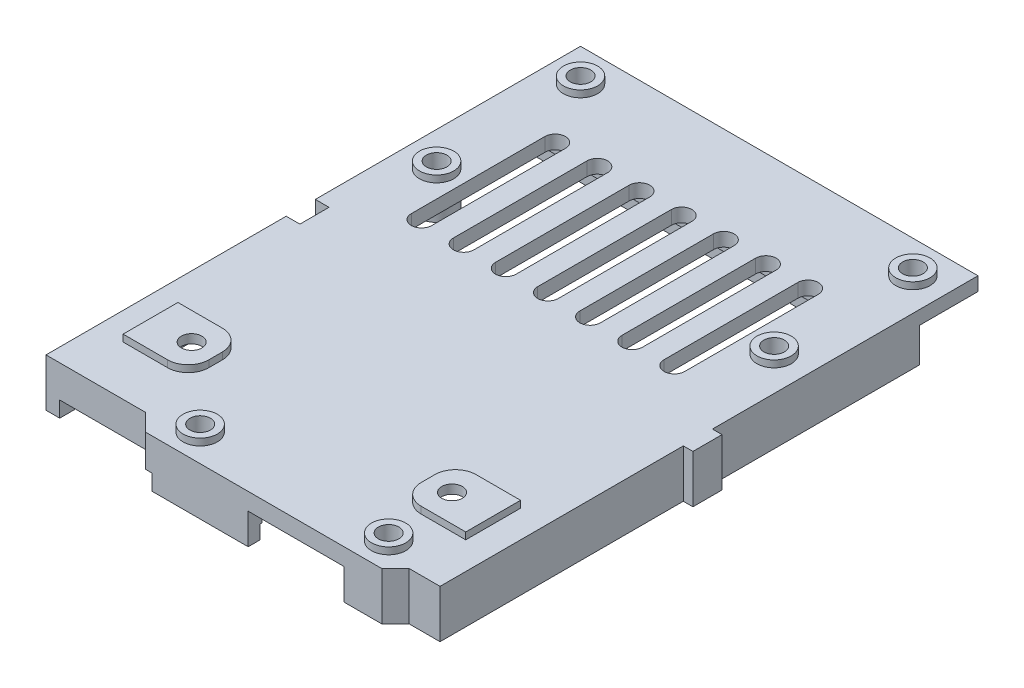
SolidWorks part; units mm, degrees
material "PVC 0.007 Plasticized"
ref_plane "Front Plane" through (0, 0, 0) normal (0, 0, 1) x (1, 0, 0)
ref_plane "Top Plane" through (0, 0, 0) normal (0, 1, 0) x (1, 0, 0)
ref_plane "Right Plane" through (0, 0, 0) normal (1, 0, 0) x (0, 0, -1)
sketch "Sketch1" plane through (0, 0, 0) normal (0, 1, 0) x (1, 0, 0)
  line L0 (0, 40.5) -> (0, 0) construction
  line L1 (-29, 40.5) -> (29, 40.5)
  line L2 (-29, 40.5) -> (-29, -40.5)
  line L3 (-29, -40.5) -> (29, -40.5)
  line L4 (29, 40.5) -> (29, -40.5)
  line L5 (-29, 40.5) -> (29, -40.5) construction
  line L6 (-29, -40.5) -> (29, 40.5) construction
  line L7 (18.2, 26.5) -> (18.2, 7) construction
  line L8 (19.7, 26.5) -> (19.7, 7)
  line L9 (16.7, 26.5) -> (16.7, 7)
  line L10 (12.05, 26.5) -> (12.05, 7) construction
  line L11 (13.55, 26.5) -> (13.55, 7)
  line L12 (10.55, 26.5) -> (10.55, 7)
  line L13 (5.9, 26.5) -> (5.9, 7) construction
  line L14 (7.4, 26.5) -> (7.4, 7)
  line L15 (4.4, 26.5) -> (4.4, 7)
  line L16 (-0.25, 26.5) -> (-0.25, 7) construction
  line L17 (1.25, 26.5) -> (1.25, 7)
  line L18 (-1.75, 26.5) -> (-1.75, 7)
  line L19 (-6.4, 26.5) -> (-6.4, 7) construction
  line L20 (-4.9, 26.5) -> (-4.9, 7)
  line L21 (-7.9, 26.5) -> (-7.9, 7)
  line L22 (-12.55, 26.5) -> (-12.55, 7) construction
  line L23 (-11.05, 26.5) -> (-11.05, 7)
  line L24 (-14.05, 26.5) -> (-14.05, 7)
  line L25 (-18.7, 26.5) -> (-18.7, 7) construction
  line L26 (-17.2, 26.5) -> (-17.2, 7)
  line L27 (-20.2, 26.5) -> (-20.2, 7)
  circle A0 centre (24.25, 35.75) radius 1.5
  circle A1 centre (-24.25, 35.75) radius 1.5
  circle A2 centre (24, 15.75) radius 1.5
  circle A3 centre (-24, 14.5) radius 1.5
  circle A4 centre (19, -26.25) radius 1.5
  circle A5 centre (19.5, -36) radius 1.5
  circle A6 centre (-8, -36) radius 1.5
  circle A7 centre (-19, -26.25) radius 1.5
  arc A8 (19.7, 26.5) -> (16.7, 26.5) centre (18.2, 26.5) ccw
  arc A9 (16.7, 7) -> (19.7, 7) centre (18.2, 7) ccw
  arc A10 (13.55, 26.5) -> (10.55, 26.5) centre (12.05, 26.5) ccw
  arc A11 (10.55, 7) -> (13.55, 7) centre (12.05, 7) ccw
  arc A12 (7.4, 26.5) -> (4.4, 26.5) centre (5.9, 26.5) ccw
  arc A13 (4.4, 7) -> (7.4, 7) centre (5.9, 7) ccw
  arc A14 (1.25, 26.5) -> (-1.75, 26.5) centre (-0.25, 26.5) ccw
  arc A15 (-1.75, 7) -> (1.25, 7) centre (-0.25, 7) ccw
  arc A16 (-4.9, 26.5) -> (-7.9, 26.5) centre (-6.4, 26.5) ccw
  arc A17 (-7.9, 7) -> (-4.9, 7) centre (-6.4, 7) ccw
  arc A18 (-11.05, 26.5) -> (-14.05, 26.5) centre (-12.55, 26.5) ccw
  arc A19 (-14.05, 7) -> (-11.05, 7) centre (-12.55, 7) ccw
  arc A20 (-17.2, 26.5) -> (-20.2, 26.5) centre (-18.7, 26.5) ccw
  arc A21 (-20.2, 7) -> (-17.2, 7) centre (-18.7, 7) ccw
  point P0 (0, 0)
  point P26 (18.2, 16.75)
  point P31 (18.2, 28)
  point P32 (18.2, 5.5)
  point P37 (12.05, 16.75)
  point P44 (5.9, 16.75)
  point P51 (-0.25, 16.75)
  point P58 (-6.4, 16.75)
  point P65 (-12.55, 16.75)
  point P72 (-18.7, 16.75)
  dimension "D3" = 3
  dimension "D6" = 3
  dimension "D9" = 3
  dimension "D12" = 3
  dimension "D17" = 3
  dimension "D26" = 3
  dimension "D1" = 81
  dimension "D2" = 58
  dimension "D4" = 48.5
  dimension "D5" = 62
  dimension "D7" = 5
  dimension "D8" = 20
  dimension "D10" = 38
  dimension "D11" = 14.25
  dimension "D13" = 4.5
  dimension "D14" = 9.5
  dimension "D15" = 27.5
  dimension "D16" = 4.5
  dimension "D18" = 22.5
  dimension "D19" = 3
  dimension "D20" = 12.5
  dimension "D21" = 9.3
  dimension "D23" = 6.15
  dimension "D24" = 5
  dimension "D25" = 21.25
  dimension "D22" = 7
extrude "Boss-Extrude1" add sketch "Sketch1" along normal blind 2
sketch "Sketch2" plane through (0, 0, 0) normal (0, -1, 0) x (1, 0, 0)
  line L0 (-29, -40.5) -> (-29, 40.5) construction
  line L1 (-29, -30) -> (29, -30)
  line L2 (-29, -30) -> (-29, -32)
  line L3 (-29, -32) -> (29, -32)
  line L4 (29, -30) -> (29, -32)
  line L5 (29, 40.5) -> (29, -40.5) construction
  line L6 (29, -40.5) -> (-29, -40.5) construction
  line L7 (24.5, 36) -> (22.5, 38)
  line L8 (29, -30) -> (27, -30)
  line L9 (29, -30) -> (29, 38)
  line L10 (29, 38) -> (27, 38)
  line L11 (27, -30) -> (27, 38)
  line L12 (29, 38) -> (24.5, 38)
  line L13 (29, 38) -> (29, 36)
  line L14 (29, 36) -> (24.5, 36)
  line L15 (24.5, 38) -> (24.5, 36)
  line L16 (22.5, 38) -> (17, 38)
  line L17 (17, 38) -> (17, 40)
  line L18 (17, 40) -> (22.5, 40)
  line L19 (22.5, 40) -> (24.5, 38)
  line L20 (-12, 40) -> (-14.5, 37.5)
  line L21 (17, 40) -> (3, 40)
  line L22 (17, 40) -> (17, 38)
  line L23 (17, 38) -> (3, 38)
  line L24 (3, 40) -> (3, 38)
  line L25 (3, 38) -> (-12, 38)
  line L26 (3, 38) -> (3, 40)
  line L27 (3, 40) -> (-12, 40)
  line L28 (-12, 38) -> (-12, 40)
  line L29 (-12, 37.5) -> (-12, 38)
  line L30 (-29, 37.5) -> (-12, 37.5)
  line L31 (-29, 37.5) -> (-29, 35.5)
  line L32 (-29, 35.5) -> (-12, 35.5)
  line L33 (-12, 37.5) -> (-12, 35.5)
  line L35 (-29, 37.5) -> (-27, 37.5)
  line L36 (-29, 37.5) -> (-29, -32)
  line L37 (-29, -32) -> (-27, -32)
  line L38 (-27, 37.5) -> (-27, -32)
  line M41 (29, -40.5) -> (29, 40.5)
  line M43 (-29, 40.5) -> (-29, -40.5)
  dimension "D1" = 2
  dimension "D2" = 10.5
  dimension "D3" = 68
  dimension "D4" = 2
  dimension "D5" = 4.5
  dimension "D6" = 2
  dimension "D7" = 45
  dimension "D8" = 2
  dimension "D9" = 5.5
  dimension "D10" = 6.5
  dimension "D11" = 2
  dimension "D12" = 14
  dimension "D13" = 15
  dimension "D14" = 45
  dimension "D15" = 2.5
  dimension "D16" = 2
  dimension "D17" = 2
extrude "Boss-Extrude2" add sketch "Sketch2" along normal blind 0.5 contours L21 L24 L23 L17 | L38 L32 L1 M43 | L1 L38 L3 M41 | L38 L1 L3 M43 | L14 L11 L1 M41 | L12 L15 L14 L11 | L14 L9 L10 L11 | L19 L18 L17 L16 L7 L15 | L28 L25 L24 L27 | L20 L30 L29 L28 | L30 L38 L32 L33 | L38 L30 L32 M43
sketch "Sketch5" plane through (0, -0.5, 0) normal (0, -1, 0) x (1, 0, 0)
  line L0 (-27, -30) -> (27, -30)
  line L1 (27, -30) -> (27, 36)
  line L2 (27, 36) -> (24.5, 36)
  line L3 (24.5, 36) -> (22.5, 38)
  line L4 (22.5, 38) -> (17, 38)
  line L5 (17, 38) -> (17, 40)
  line L6 (-11, 38) -> (-11, 40)
  line L7 (-27, 35.5) -> (-27, 37.5)
  line L8 (-27, 35.5) -> (-12, 35.5)
  line L9 (-12, 35.5) -> (-12, 38)
  line L10 (-12, 38) -> (3, 38)
  line L11 (3, 38) -> (3, 40)
  line L12 (-27, 35.5) -> (-27, -30)
  line L16 (22.5, 40) -> (-12, 40)
  line L17 (-12, 40) -> (-14.5, 37.5)
  line L18 (-14.5, 37.5) -> (-29, 37.5)
  line L19 (-29, 37.5) -> (-29, -32)
  line L20 (-29, -32) -> (29, -32)
  line L21 (29, -32) -> (29, 38)
  line L22 (29, 38) -> (24.5, 38)
  line L23 (24.5, 38) -> (22.5, 40)
  line L24 (22.5, 40) -> (-12, 40)
  line L25 (-12, 40) -> (-14.5, 37.5)
  line L26 (-14.5, 37.5) -> (-29, 37.5)
  line L27 (-29, 37.5) -> (-29, -32)
  line L28 (-29, -32) -> (29, -32)
  line L29 (29, -32) -> (29, 38)
  line L30 (29, 38) -> (24.5, 38)
  line L31 (24.5, 38) -> (22.5, 40)
  line M10 (27, -30) -> (-27, -30)
  line M11 (-27, -30) -> (-27, 35.5)
  line M12 (-27, 35.5) -> (-12, 35.5)
  line M13 (-12, 35.5) -> (-12, 38)
  line M14 (-12, 38) -> (22.5, 38)
  line M15 (22.5, 38) -> (24.5, 36)
  line M16 (24.5, 36) -> (27, 36)
  line M17 (27, 36) -> (27, -30)
  line M18 (22.5, 40) -> (-12, 40)
  line M19 (-12, 40) -> (-14.5, 37.5)
  line M20 (-14.5, 37.5) -> (-29, 37.5)
  line M21 (-29, 37.5) -> (-29, -32)
  line M22 (-29, -32) -> (29, -32)
  line M23 (29, -32) -> (29, 38)
  line M24 (29, 38) -> (24.5, 38)
  line M25 (24.5, 38) -> (22.5, 40)
  dimension "D2" = 1
  dimension "D1" = 0
extrude "Boss-Extrude3" add sketch "Sketch5" along normal blind 4.5 contours L6 L5 M14 M18 M19 M20 M21 M22 M23 M24 M25 M15 M16 M17 M10 M11 M12 M13 | L11 L6 M14 M18
sketch "Sketch6" plane through (0, 0, 0) normal (0, -1, 0) x (1, 0, 0)
  line L16 (-11, 38) -> (-11, 40)
  line L17 (-11, 40) -> (-12, 40)
  line L18 (-12, 40) -> (-14.5, 37.5)
  line L19 (-14.5, 37.5) -> (-27, 37.5)
  line L20 (-27, 37.5) -> (-27, 35.5)
  line L21 (-27, 35.5) -> (-12, 35.5)
  line L22 (-12, 35.5) -> (-12, 38)
  line L23 (-12, 38) -> (-11, 38)
  line L24 (-11, 38) -> (-11, 40)
  line L25 (-11, 40) -> (-12, 40)
  line L26 (-12, 40) -> (-14.5, 37.5)
  line L27 (-14.5, 37.5) -> (-27, 37.5)
  line L28 (-27, 37.5) -> (-27, 35.5)
  line L29 (-27, 35.5) -> (-12, 35.5)
  line L30 (-12, 35.5) -> (-12, 38)
  line L31 (-12, 38) -> (-11, 38)
  dimension "D1" = 0
extrude "Boss-Extrude4" add sketch "Sketch6" along normal blind 2.7
sketch "Sketch7" plane through (0, 0, 0) normal (0, -1, 0) x (1, 0, 0)
  line L1 (-25, 30.25) -> (-15.5, 30.25)
  line L2 (-25, 30.25) -> (-25, 22.25)
  line L3 (-25, 22.25) -> (-15.5, 22.25)
  line L4 (-15.5, 30.25) -> (-15.5, 22.25)
  line L5 (-27, -30) -> (-27, 37.5) construction
  line L6 (0, 0) -> (0, 40.5) construction
  line L7 (-29, 40.5) -> (29, 40.5) construction
  line L8 (15.5, 30.25) -> (15.5, 22.25)
  line L9 (25, 22.25) -> (15.5, 22.25)
  line L10 (25, 30.25) -> (25, 22.25)
  line L11 (25, 30.25) -> (15.5, 30.25)
  circle A1 centre (-19, 26.25) radius 1.5
  arc A2 (-18.5, 30.25) -> (-15.5, 27.25) centre (-18.5, 27.25) cw
  arc A3 (-15.5, 25.25) -> (-18.5, 22.25) centre (-18.5, 25.25) cw
  arc A4 (15.5, 25.25) -> (18.5, 22.25) centre (18.5, 25.25) ccw
  arc A5 (18.5, 30.25) -> (15.5, 27.25) centre (18.5, 27.25) ccw
  circle A6 centre (19, 26.25) radius 1.5
  point P10 (-15.5, 26.25)
  circle M32 centre (19, 26.25) radius 1.5
  circle M35 centre (-19, 26.25) radius 1.5
  dimension "D4" = 3
  dimension "D5" = 3
  dimension "D6" = 3
  dimension "D1" = 8
  dimension "D2" = 9.5
  dimension "D3" = 2
extrude "Cut-Extrude1" cut sketch "Sketch7" against normal blind 1.7 contours A3 L4 A2 L1 L2 L3 M35 | L11 A5 L8 A4 L9 L10 M32
sketch "Sketch8" plane through (0, 2, 0) normal (0, 1, 0) x (1, 0, 0)
  line L0 (-25, -26.25) -> (-19, -26.25) construction
  line L1 (-25, -22.25) -> (-15.5, -22.25)
  line L2 (-25, -22.25) -> (-25, -30.25)
  line L3 (-25, -30.25) -> (-15.5, -30.25)
  line L4 (-15.5, -22.25) -> (-15.5, -30.25)
  line L5 (15.5, -22.25) -> (25, -22.25)
  line L6 (15.5, -22.25) -> (15.5, -30.25)
  line L7 (15.5, -30.25) -> (25, -30.25)
  line L8 (25, -22.25) -> (25, -30.25)
  line L9 (0, -40.5) -> (0, 0) construction
  arc A18 (-18.5, -22.25) -> (-15.5, -25.25) centre (-18.5, -25.25) cw
  arc A19 (-18.5, -30.25) -> (-15.5, -27.25) centre (-18.5, -27.25) ccw
  arc A20 (18.5, -22.25) -> (15.5, -25.25) centre (18.5, -25.25) ccw
  arc A21 (18.5, -30.25) -> (15.5, -27.25) centre (18.5, -27.25) cw
  circle M6 centre (19, -26.25) radius 1.5
  circle M16 centre (-19, -26.25) radius 1.5
  dimension "D1" = 3
extrude "Boss-Extrude5" add sketch "Sketch8" along normal blind 1 contours A21 L7 L8 L5 A20 L6 M6 | L3 A19 L4 A18 L1 L2 M16
sketch "Sketch9" plane through (0, 2, 0) normal (0, 1, 0) x (1, 0, 0)
  line L0 (0, -40.5) -> (0, 0) construction
  line L1 (-29, -40.5) -> (29, -40.5) construction
  circle A0 centre (-24.25, 35.75) radius 1.5
  circle A1 centre (-24.25, 35.75) radius 2.5
  circle A2 centre (-24, 14.5) radius 1.5
  circle A3 centre (-24, 14.5) radius 2.5
  circle A4 centre (-8, -36) radius 1.5
  circle A5 centre (-8, -36) radius 2.5
  circle A6 centre (19.5, -36) radius 1.5
  circle A7 centre (19.5, -36) radius 2.5
  circle A8 centre (24, 15.75) radius 2.5
  circle A9 centre (24, 15.75) radius 1.5
  circle A10 centre (24.25, 35.75) radius 2.5
  circle A11 centre (24.25, 35.75) radius 1.5
  circle A12 centre (24, 15.75) radius 1.5 construction
  dimension "D1" = 5
  dimension "D2" = 3
  dimension "D3" = 5
  dimension "D4" = 3
  dimension "D5" = 5
  dimension "D6" = 3
  dimension "D7" = 5
  dimension "D8" = 3
  dimension "D9" = 3
  dimension "D10" = 5
extrude "Boss-Extrude6" add sketch "Sketch9" along normal blind 1
sketch "Sketch10" plane through (0, 0, 0) normal (0, -1, 0) x (1, 0, 0)
  line L0 (-27, 35.5) -> (-27, -30) construction
  line L1 (-24, -12) -> (-27, -12)
  line L2 (-24, -12) -> (-24, -17)
  line L3 (-24, -17) -> (-27, -17)
  line L4 (-27, -12) -> (-27, -17)
  line L5 (-11, 38) -> (3, 38) construction
  line L6 (-10.5, 36) -> (-5.5, 36)
  line L7 (-10.5, 36) -> (-10.5, 38)
  line L8 (-10.5, 38) -> (-5.5, 38)
  line L9 (-5.5, 36) -> (-5.5, 38)
  line L10 (22.5, 38) -> (-12, 38) construction
  line L11 (17, 36) -> (22, 36)
  line L12 (17, 36) -> (17, 38)
  line L13 (17, 38) -> (22, 38)
  line L14 (22, 36) -> (22, 38)
  line L15 (0, 0) -> (0, 38) construction
  line L16 (27, -13.25) -> (27, -18.25)
  line L17 (24, -18.25) -> (27, -18.25)
  line L18 (24, -13.25) -> (24, -18.25)
  line L19 (24, -13.25) -> (27, -13.25)
  line L21 (27, -30) -> (27, 36) construction
  circle A0 centre (-24, -14.5) radius 1.5
  circle A1 centre (-24, -14.5) radius 2.5
  circle A2 centre (-8, 36) radius 1.5
  circle A3 centre (-8, 36) radius 2.5
  circle A4 centre (19.5, 36) radius 1.5
  circle A5 centre (19.5, 36) radius 2.5
  circle A6 centre (24, -15.75) radius 2.5
  circle A7 centre (24, -15.75) radius 1.5
  circle A8 centre (24, -15.75) radius 1.5 construction
  point P43 (24, -15.75)
  dimension "D1" = 5
  dimension "D2" = 3
  dimension "D3" = 5
  dimension "D4" = 3
  dimension "D5" = 3
  dimension "D6" = 5
  dimension "D7" = 5
  dimension "D8" = 3
extrude "Boss-Extrude7" add sketch "Sketch10" along normal blind 3 contours L6 A3 A2 | L6 A3 L8 A2 | A3 L9 L8 | A3 L8 L7 | A5 L14 L13 | L11 A5 L13 A4 | L11 A5 A4 | A5 L13 L12 | L19 A6 L17 L16 | L18 A7 A6 | L18 A7 A6 | A1 L1 L4 L3 | L2 A1 A0 | L2 A1 A0
sketch "Sketch11" plane through (0, -5, 0) normal (0, -1, 0) x (1, 0, 0)
  line L1 (-29, 2.45) -> (-27, 2.45)
  line L2 (-29, 2.45) -> (-29, -1.8)
  line L3 (-29, -1.8) -> (-27, -1.8)
  line L4 (-27, 2.45) -> (-27, -1.8)
  line L5 (-27, 35.5) -> (-27, -12) construction
  line L6 (-29, -32) -> (29, -32) construction
  dimension "D1" = 30.2
  dimension "D2" = 4.25
extrude "Cut-Extrude2" cut sketch "Sketch11" against normal through all
sketch "Sketch12" plane through (0, 0, 0) normal (0, -1, 0) x (1, 0, 0)
  line L0 (-27, 35.5) -> (-27, 2.45) construction
  line L1 (-27, 3.325) -> (-25.3, 3.325)
  line L2 (-27, 3.325) -> (-27, -2.675)
  line L3 (-27, -2.675) -> (-25.3, -2.675)
  line L4 (-25.3, 3.325) -> (-25.3, -2.675)
  line L5 (-29, 2.45) -> (-29, -1.8) construction
  point P10 (-25.3, 0.325)
  point P11 (-29, 0.325)
  dimension "D1" = 1.7
  dimension "D2" = 6
extrude "Boss-Extrude8" add sketch "Sketch12" along normal blind 3
sketch "Sketch13" plane through (0, -5, 0) normal (0, -1, 0) x (1, 0, 0)
  line L0 (29, -32) -> (29, 38) construction
  line L1 (29, 2.5) -> (30.4, 2.5)
  line L2 (29, 2.5) -> (29, -1.75)
  line L3 (29, -1.75) -> (30.4, -1.75)
  line L4 (30.4, 2.5) -> (30.4, -1.75)
  line L5 (-29, -32) -> (29, -32) construction
  dimension "D1" = 34.5
  dimension "D2" = 4.25
  dimension "D3" = 1.4
extrude "Boss-Extrude9" add sketch "Sketch13" against normal up to surface (7 mm away) up to face at (-14, 2, 0.1625)
sketch "Sketch14" plane through (0, -2.7, 0) normal (0, -1, 0) x (1, 0, 0)
  line L0 (-27, 35.5) -> (-12, 35.5) construction
  line L1 (-12, 38) -> (-9.5, 38)
  line L2 (-12, 38) -> (-12, 35.5)
  line L3 (-12, 35.5) -> (-9.5, 35.5)
  line L4 (-9.5, 38) -> (-9.5, 35.5)
  circle A0 centre (-8, 36) radius 1.5 construction
extrude "Boss-Extrude10" add sketch "Sketch14" against normal up to surface (2.7 mm away) up to face at (-12.55, 0, -16.75)
sketch "Sketch15" plane through (0, 0, 0) normal (0, -1, 0) x (1, 0, 0)
  line L0 (-29, 40.5) -> (-29, 37.5)
  line L1 (-29, 37.5) -> (-14.5, 37.5)
  line L2 (-14.5, 37.5) -> (-12, 40)
  line L3 (-12, 40) -> (22.5, 40)
  line L4 (22.5, 40) -> (24.5, 38)
  line L5 (24.5, 38) -> (29, 38)
  line L6 (29, 38) -> (29, 40.5)
  line L7 (29, 40.5) -> (-29, 40.5)
extrude "Cut-Extrude3" cut sketch "Sketch15" against normal through all
sketch "Sketch17" plane through (0, -5, 0) normal (0, -1, 0) x (1, 0, 0)
  line L0 (27, 36) -> (27, -30) construction
  line L1 (-10.5, 38.29) -> (27, 38.29)
  line L2 (-10.5, 38.29) -> (-10.5, -30.29)
  line L3 (-10.5, -30.29) -> (27, -30.29)
  line L4 (27, 38.29) -> (27, -30.29)
  line L5 (-10.5, 36) -> (-10.5, 38) construction
  line L6 (3, 38) -> (3, -30) construction
  line L7 (-27, -30) -> (27, -30) construction
  line L8 (-10.5, -30.29) -> (-27, -30.29)
  line L9 (-27, -30.29) -> (-27, -26.2816)
  line L10 (-27, -17) -> (-27, -30) construction
  line L11 (-27, -26.2816) -> (-10.5, -26.2816)
  line L12 (-10.5, 38) -> (22.5, 38)
  line L13 (22.5, 38) -> (22.5, 38.29)
  line L14 (17, 38) -> (22.5, 38) construction
  line L15 (-11, 38) -> (3, 38) construction
  line L16 (-10.5, 38.29) -> (-11, 38.29)
  line L17 (-10.5, 38.29) -> (-10.5, 38)
  line L18 (-10.5, 38) -> (-11, 38)
  line L19 (-11, 38.29) -> (-11, 38)
  line L20 (-11, 38) -> (-11, 40) construction
  point P13 (3, 4)
  point P14 (27, 4)
  line M15 (17, 40) -> (17, 38)
  line M16 (17, 38) -> (22.5, 38)
  line M20 (27, -30) -> (-27, -30)
  dimension "D1" = 68.58
extrude "Cut-Extrude4" cut sketch "Sketch17" against normal up to surface (2 mm away) contours L2 L12 L1 M15 | L13 L1 M16 M15 | L4 L2 L3 M20 | L9 L8 L2 M20 | L16 L19 L18 L2 up to face at (-8, -3, 34.5)
